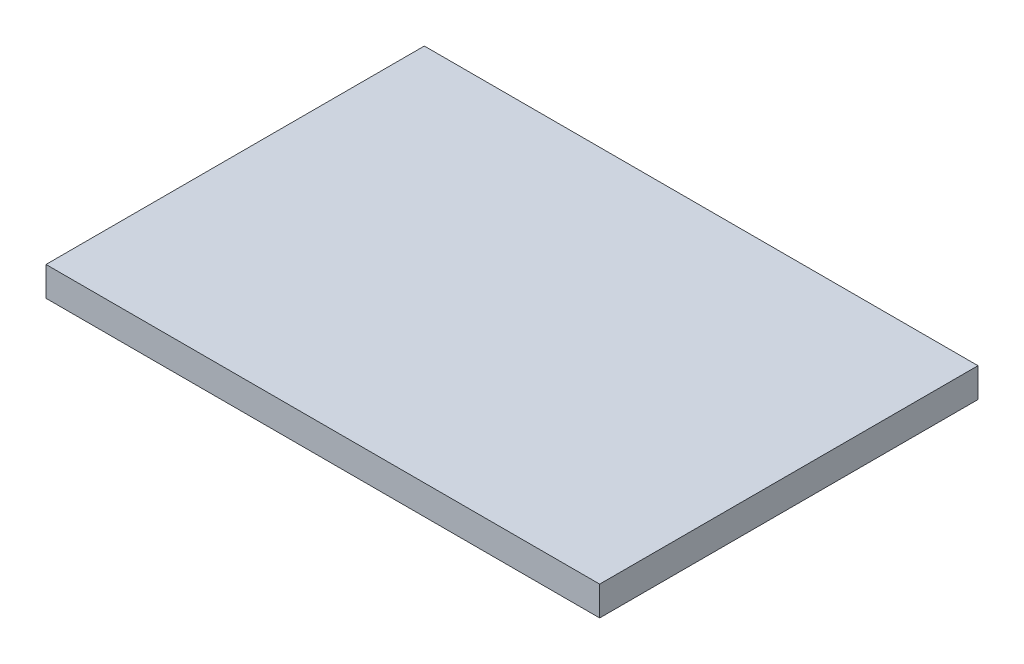
SolidWorks part; units mm, degrees
ref_plane "Front Plane" through (0, 0, 0) normal (0, 0, 1) x (1, 0, 0)
ref_plane "Top Plane" through (0, 0, 0) normal (0, 1, 0) x (1, 0, 0)
ref_plane "Right Plane" through (0, 0, 0) normal (1, 0, 0) x (0, 0, -1)
sketch "Sketch3" plane through (0, 0, 0) normal (0, 1, 0) x (1, 0, 0)
  line L1 (0, 0) -> (30, 0)
  line L2 (0, 0) -> (0, 20.5)
  line L3 (0, 20.5) -> (30, 20.5)
  line L4 (30, 0) -> (30, 20.5)
  dimension "D1" = 20.5
  dimension "D2" = 30
extrude "Boss-Extrude1" add sketch "Sketch3" along normal blind 1.59
sketch "Sketch7" plane through (0, 1.59, 0) normal (0, 1, 0) x (1, 0, 0)
  line L0 (0, 3.5) -> (30, 3.5)
  line L1 (0, 17) -> (30, 17)
  line L2 (0, 0) -> (30, 0) construction
  line L3 (26.5, 17) -> (26.5, 7.5)
  line L5 (30, 0) -> (30, 20.5) construction
  line L6 (0, 20.5) -> (0, 0) construction
  line L7 (0, 7.5) -> (26.5, 7.5)
  circle A0 centre (4, 12.25) radius 0.35
  circle A1 centre (4, 5.5) radius 0.35
  dimension "D5" = 0.7
  dimension "D6" = 0.7
  dimension "D1" = 3.5
  dimension "D2" = 3.5
  dimension "D3" = 4
  dimension "D4" = 9.5
  dimension "D7" = 4
  dimension "D8" = 4.75
  dimension "D9" = 2
